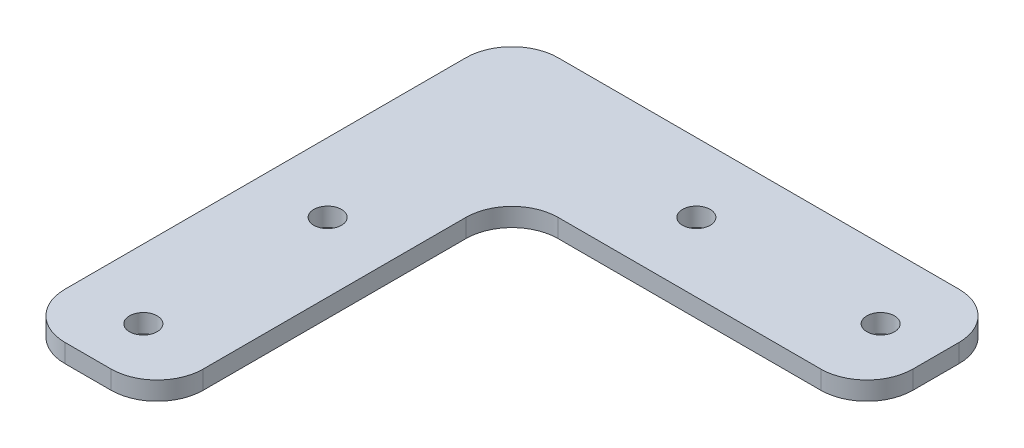
SolidWorks part; units mm, degrees
material "Carbon Fiber"
ref_plane "Front Plane" through (0, 0, 0) normal (0, 0, 1) x (1, 0, 0)
ref_plane "Top Plane" through (0, 0, 0) normal (0, 1, 0) x (1, 0, 0)
ref_plane "Right Plane" through (0, 0, 0) normal (1, 0, 0) x (0, 0, -1)
sketch "Sketch1" plane through (0, 0, 0) normal (0, 1, 0) x (1, 0, 0)
  line L0 (0, -40) -> (0, 0) construction
  line L1 (0, 0) -> (7.5, -7.5) construction
  line L2 (7.5, -7.5) -> (7.5, -46)
  line L3 (7.5, -46) -> (-7.5, -46)
  line L4 (-7.5, -46) -> (-7.5, 7.5)
  line L5 (46, 7.5) -> (-7.5, 7.5)
  line L6 (46, -7.5) -> (46, 7.5)
  line L7 (7.5, -7.5) -> (46, -7.5)
  circle A0 centre (0, -40) radius 1.5
  circle A1 centre (0, -20) radius 1.5
  circle A2 centre (20, 0) radius 1.5
  circle A3 centre (40, 0) radius 1.5
  dimension "D2" = 3
  dimension "D3" = 15
  dimension "D1" = 45
  dimension "D4" = 6
  dimension "D5" = 20
  dimension "D6" = 20
extrude "Boss-Extrude1" add sketch "Sketch1" along normal blind 2
fillet "Fillet1" radius 5 6 edges at (7.5, 1, 46) (-7.5, 1, 46) (-7.5, 1, -7.5) (46, 1, -7.5) (46, 1, 7.5) (7.5, 1, 7.5)
